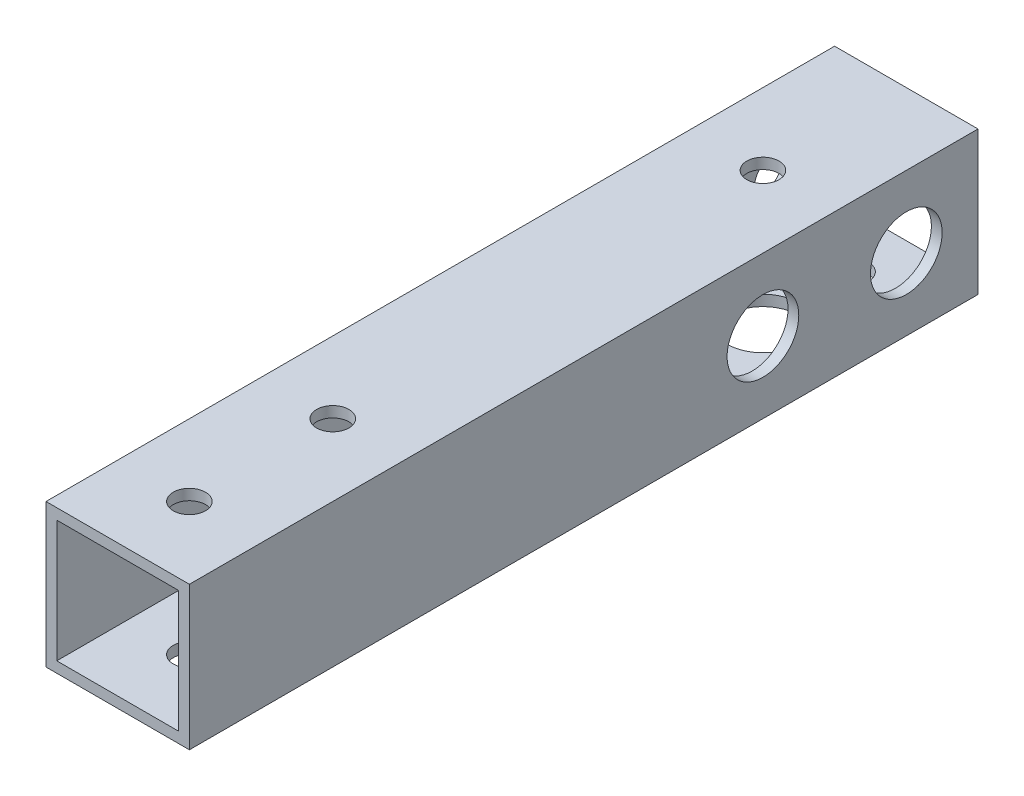
SolidWorks part; units mm, degrees
material "1060 合金"
ref_plane "正面" through (0, 0, 0) normal (0, 0, 1) x (1, 0, 0)
ref_plane "平面" through (0, 0, 0) normal (0, 1, 0) x (1, 0, 0)
ref_plane "右側面" through (0, 0, 0) normal (1, 0, 0) x (0, 0, -1)
sketch "ｽｹｯﾁ1" plane through (0, 0, 0) normal (0, 0, 1) x (1, 0, 0)
  line L1 (-10, -10) -> (10, -10)
  line L2 (-10, -10) -> (-10, 10)
  line L3 (-10, 10) -> (10, 10)
  line L4 (10, -10) -> (10, 10)
  line L5 (-10, -10) -> (10, 10) construction
  line L6 (-10, 10) -> (10, -10) construction
  line L7 (-8.5, -8.5) -> (8.5, -8.5)
  line L8 (-8.5, -8.5) -> (-8.5, 8.5)
  line L9 (-8.5, 8.5) -> (8.5, 8.5)
  line L10 (8.5, -8.5) -> (8.5, 8.5)
  line L11 (-8.5, -8.5) -> (8.5, 8.5) construction
  line L12 (-8.5, 8.5) -> (8.5, -8.5) construction
  point P0 (0, 0)
  point P6 (0, 0)
  dimension "D1" = 1.5
  dimension "D2" = 20
  dimension "D3" = 20
extrude "ﾎﾞｽ - 押し出し1" add sketch "ｽｹｯﾁ1" along normal blind 110
sketch "ｽｹｯﾁ2" plane through (10, 0, 0) normal (1, 0, 0) x (0, 0, -1)
  line L0 (-110, -10) -> (0, -10) construction
  circle A9 centre (-30, 0) radius 2.7
  circle A10 centre (-10, 0) radius 2.7
  dimension "D1" = 20
  dimension "D8" = 5.4
  dimension "D4" = 10
  dimension "D5" = 10
  dimension "5.4" = 5.4
  dimension "D9" = 10
extrude "ｶｯﾄ - 押し出し1" cut sketch "ｽｹｯﾁ2" against normal blind 25
sketch "ｽｹｯﾁ3" plane through (0, 10, 0) normal (0, 1, 0) x (1, 0, 0)
  line L0 (10, -110) -> (-10, -110) construction
  line L1 (-10, -110) -> (-10, 0) construction
  circle A0 centre (0, -100) radius 2.25
  circle A4 centre (0, -80) radius 2.25
  circle A5 centre (0, -20) radius 2.25
  dimension "D1" = 4.5
  dimension "D2" = 10
  dimension "D3" = 10
  dimension "D6" = 2
  dimension "D7" = 20
  dimension "D5" = 20
  dimension "D4" = 2
extrude "ｶｯﾄ - 押し出し2" cut sketch "ｽｹｯﾁ3" against normal blind 20
sketch "ｽｹｯﾁ4" plane through (0, -10, 0) normal (0, -1, 0) x (-1, 0, 0)
  line L0 (10, 0) -> (-10, 0) construction
  circle A1 centre (0, -7.5) radius 2.25
  point P0 (0, 0)
  dimension "D2" = 7.5
  dimension "D6" = 4.5
extrude "ｶｯﾄ - 押し出し3" cut sketch "ｽｹｯﾁ4" against normal blind 5
sketch "ｽｹｯﾁ5" plane through (0, -10, 0) normal (0, -1, 0) x (-1, 0, 0)
  circle A0 centre (0, -20) radius 5
  dimension "D1" = 10
extrude "ｶｯﾄ - 押し出し4" cut sketch "ｽｹｯﾁ5" against normal blind 10
sketch "ｽｹｯﾁ6" plane through (10, 0, 0) normal (1, 0, 0) x (0, 0, -1)
  circle A0 centre (-10, 0) radius 5
  circle A1 centre (-30, 0) radius 5
  dimension "D1" = 10
  dimension "D2" = 10
extrude "ｶｯﾄ - 押し出し5" cut sketch "ｽｹｯﾁ6" against normal blind 10
